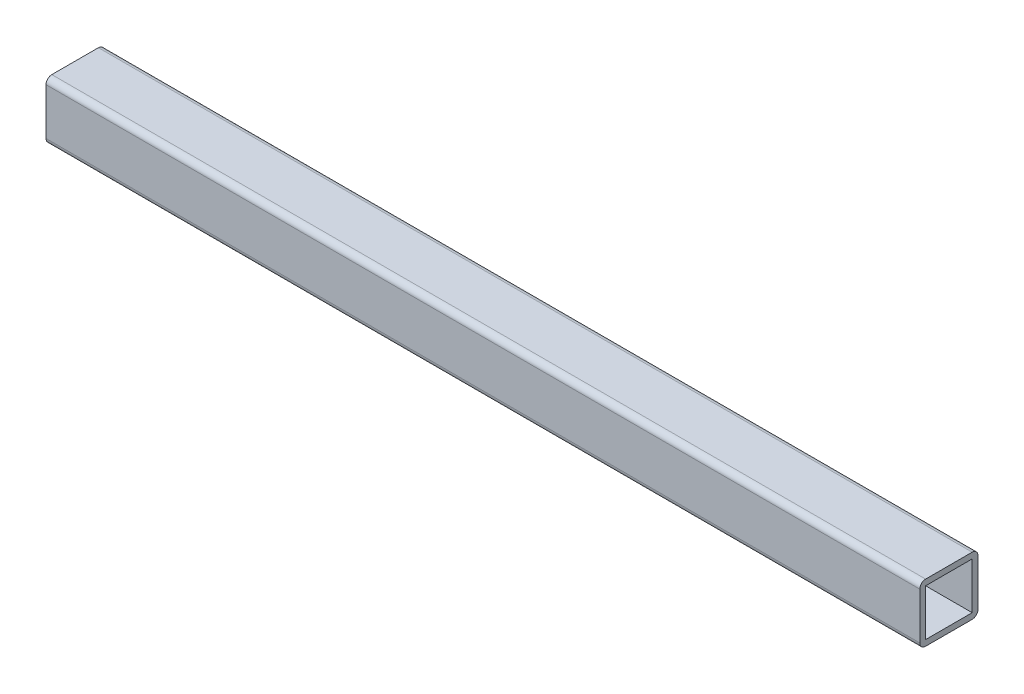
SolidWorks part; units mm, degrees
ref_plane "Front Plane" through (0, 0, 0) normal (0, 0, 1) x (1, 0, 0)
ref_plane "Top Plane" through (0, 0, 0) normal (0, 1, 0) x (1, 0, 0)
ref_plane "Right Plane" through (0, 0, 0) normal (1, 0, 0) x (0, 0, -1)
sketch "Sketch1" plane through (0, 0, 0) normal (0, 0, 1) x (1, 0, 0)
  line L0 (-20, 0) -> (-980, 0) construction
  line L1 (-289.9, -292) -> (-590.1, -292)
  line L2 (-289.9, -292) -> (-289.9, -312)
  line L3 (-289.9, -312) -> (-590.1, -312)
  line L4 (-590.1, -292) -> (-590.1, -312)
  line L5 (-590.1, 0) -> (-590.1, -1080) construction
  line L6 (-289.9, -1080) -> (-289.9, 0) construction
  dimension "D1" = 20
  dimension "D2" = 292
extrude "Boss-Extrude1" add sketch "Sketch1" against normal blind 20
fillet "Fillet1" radius 2 4 edges at (-440, -292, -20) (-440, -312, -20) (-440, -292, 0) (-440, -312, 0)
sketch "Sketch2" plane through (-289.9, 0, 0) normal (1, 0, 0) x (0, 0, -1)
  line L8 (18, -310) -> (18, -294)
  line L9 (18, -294) -> (2, -294)
  line L10 (2, -294) -> (2, -310)
  line L11 (2, -310) -> (18, -310)
  line L12 (18, -310) -> (18, -294)
  line L13 (18, -294) -> (2, -294)
  line L14 (2, -294) -> (2, -310)
  line L15 (2, -310) -> (18, -310)
  dimension "D1" = 2
extrude "Cut-Extrude1" cut sketch "Sketch2" against normal through all
